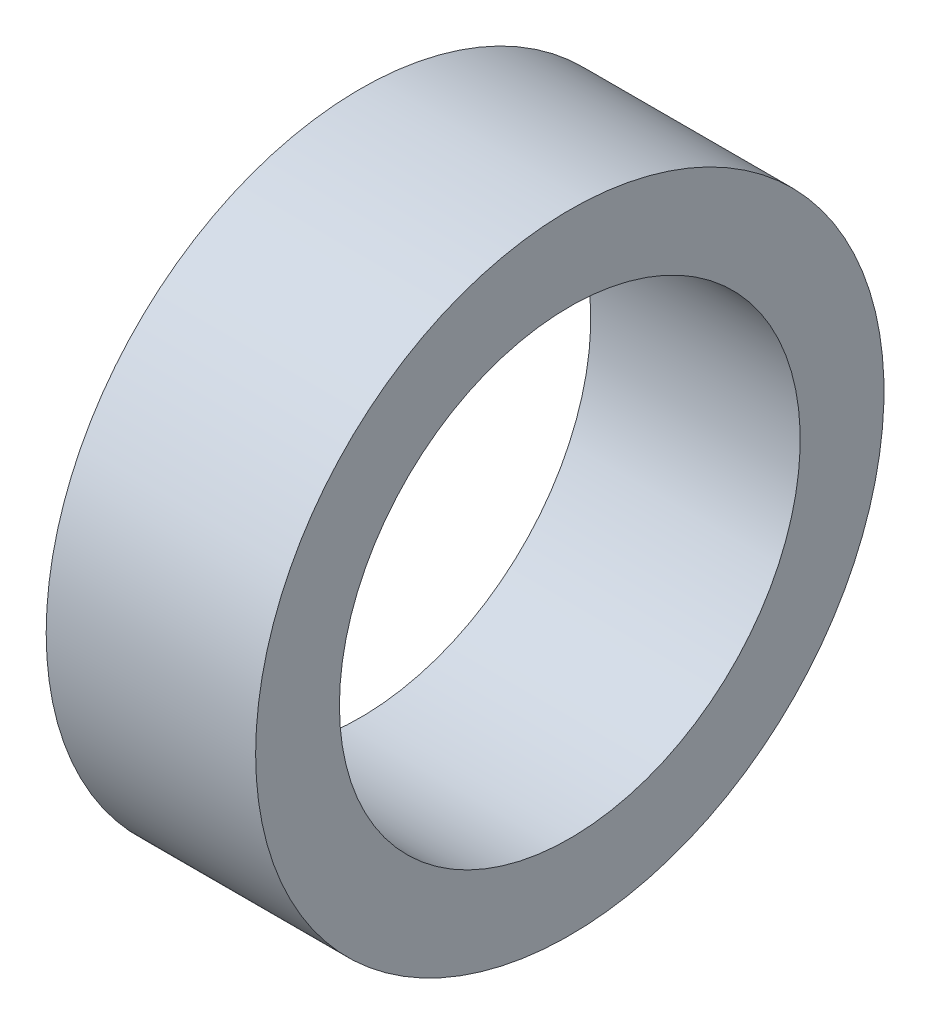
SolidWorks part; units mm, degrees
ref_plane "Front Plane" through (0, 0, 0) normal (0, 0, 1) x (1, 0, 0)
ref_plane "Top Plane" through (0, 0, 0) normal (0, 1, 0) x (1, 0, 0)
ref_plane "Right Plane" through (0, 0, 0) normal (1, 0, 0) x (0, 0, -1)
sketch "Sketch2" plane through (0, 0, 0) normal (0, 1, 0) x (1, 0, 0)
  line L0 (-12.7, 38.1) -> (-12.7, 27.94)
  line L1 (-12.7, 27.94) -> (12.7, 27.94)
  line L2 (12.7, 27.94) -> (12.7, 38.1)
  line L3 (12.7, 38.1) -> (-12.7, 38.1)
  point P2 (0, 38.1)
  dimension "D1" = 27.94
  dimension "D2" = 10.16
  dimension "D3" = 25.4
  dimension "D4" = 12.7
ref_axis "Axis1" through (-13.97, 0, 0) along (1, 0, 0)
revolve "Revolve1" add sketch "Sketch2" angle 360 about axis through (-13.97, 0, 0) along (1, 0, 0)
